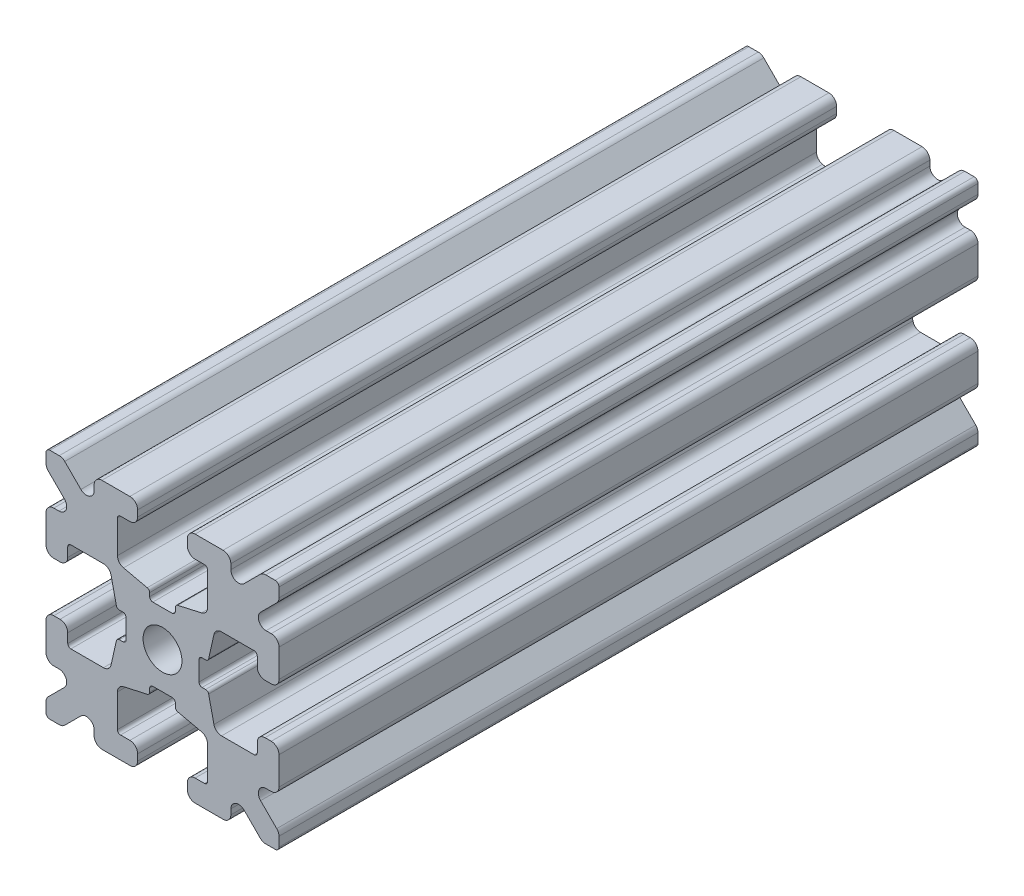
SolidWorks part; units mm, degrees
ref_plane "Front Plane" through (0, 0, 0) normal (0, 0, 1) x (1, 0, 0)
ref_plane "Top Plane" through (0, 0, 0) normal (0, 1, 0) x (1, 0, 0)
ref_plane "Right Plane" through (0, 0, 0) normal (1, 0, 0) x (0, 0, -1)
sketch "Sketch1" plane through (0, 0, 0) normal (0, 0, 1) x (1, 0, 0)
  line L1 (-7.5, -7.5) -> (7.5, -7.5)
  line L2 (-7.5, -7.5) -> (-7.5, 7.5)
  line L3 (-7.5, 7.5) -> (7.5, 7.5)
  line L4 (7.5, -7.5) -> (7.5, 7.5)
  line L5 (-7.5, -7.5) -> (7.5, 7.5) construction
  line L6 (-7.5, 7.5) -> (7.5, -7.5) construction
  circle A0 centre (0, 0) radius 1.25
  point P0 (0, 0)
  dimension "D2" = 2.5
  dimension "D1" = 15
extrude "Boss-Extrude1" add sketch "Sketch1" along normal mid plane 45
fillet "Fillet1" radius 0.25 4 edges at (7.5, -7.5, 0) (-7.5, -7.5, 0) (7.5, 7.5, 0) (-7.5, 7.5, 0)
sketch "Sketch2" plane through (0, 0, 22.5) normal (0, 0, 1) x (1, 0, 0)
  line L0 (-7.5, 7.25) -> (-7.5, -7.25) construction
  line L1 (-7.5, 1.6) -> (-6.1, 1.6)
  line L2 (-7.5, 1.6) -> (-7.5, -1.6)
  line L3 (-7.5, -1.6) -> (-6.1, -1.6)
  line L4 (-6.1, 1.6) -> (-6.1, 2.9)
  line L5 (0, 0) -> (-12.1036, 0) construction
  line L6 (-6.1, -2.9) -> (-3.4, -2.9)
  line L7 (0, 0) -> (-7.25, 7.25) construction
  line L8 (-6.1, 2.9) -> (-3.4, 2.9)
  line L9 (-3.4, -2.9) -> (-3.4, 2.9)
  line L10 (55, 0) -> (-55, 0) construction
  line L11 (-6.1, -2.9) -> (-6.1, -1.6)
  line L12 (2.9, 6.1) -> (1.6, 6.1)
  line L13 (2.9, 3.4) -> (-2.9, 3.4)
  line L14 (-2.9, 6.1) -> (-2.9, 3.4)
  line L15 (2.9, 6.1) -> (2.9, 3.4)
  line L16 (-1.6, 6.1) -> (-2.9, 6.1)
  line L17 (1.6, 7.5) -> (1.6, 6.1)
  line L18 (-1.6, 7.5) -> (1.6, 7.5)
  line L19 (-1.6, 7.5) -> (-1.6, 6.1)
  line L20 (-1.6, -7.5) -> (-1.6, -6.1)
  line L21 (-1.6, -7.5) -> (1.6, -7.5)
  line L22 (1.6, -7.5) -> (1.6, -6.1)
  line L23 (-1.6, -6.1) -> (-2.9, -6.1)
  line L24 (2.9, -6.1) -> (2.9, -3.4)
  line L25 (-2.9, -6.1) -> (-2.9, -3.4)
  line L26 (2.9, -3.4) -> (-2.9, -3.4)
  line L27 (2.9, -6.1) -> (1.6, -6.1)
  line L28 (6.1, -2.9) -> (6.1, -1.6)
  line L29 (3.4, -2.9) -> (3.4, 2.9)
  line L30 (6.1, 2.9) -> (3.4, 2.9)
  line L31 (6.1, -2.9) -> (3.4, -2.9)
  line L32 (6.1, 1.6) -> (6.1, 2.9)
  line L33 (7.5, -1.6) -> (6.1, -1.6)
  line L34 (7.5, 1.6) -> (7.5, -1.6)
  line L35 (7.5, 1.6) -> (6.1, 1.6)
  dimension "D1" = 3.2
  dimension "D2" = 5.8
  dimension "D3" = 1.4
  dimension "D4" = 2.7
extrude "Cut-Extrude1" cut sketch "Sketch2" against normal through all
sketch "Sketch4" plane through (0, 0, 22.5) normal (0, 0, 1) x (1, 0, 0)
  line L0 (-3.4, 2.9) -> (-2.75, 0)
  line L1 (55, 0) -> (-55, 0) construction
  line L2 (-2.75, 0) -> (-3.4, -2.9)
  line L3 (-3.4, -2.9) -> (-3.4, 2.9) construction
  line L4 (-3.4, 2.9) -> (-3.4, -2.9)
  line L5 (-2.9, 3.4) -> (0, 2.75)
  line L6 (0, 2.75) -> (2.9, 3.4)
  line L7 (2.9, 3.4) -> (-2.9, 3.4)
  line L8 (3.4, 2.9) -> (2.75, 0)
  line L9 (2.75, 0) -> (3.4, -2.9)
  line L10 (3.4, -2.9) -> (3.4, 2.9)
  line L11 (-2.9, -3.4) -> (0, -2.75)
  line L12 (0, -2.75) -> (2.9, -3.4)
  line L13 (2.9, -3.4) -> (-2.9, -3.4)
  circle A2 centre (0, 0) radius 2.75
  circle A3 centre (0, 0) radius 2.75 construction
  dimension "D1" = 1.5
extrude "Cut-Extrude3" cut sketch "Sketch4" against normal through all
fillet "Fillet3" radius 0.5 16 edges at (-6.1, -1.6, 0) (-7.5, -1.6, 0) (-6.1, 1.6, 0) (-7.5, 1.6, 0) (-1.6, -7.5, 0) (-1.6, -6.1, 0) (1.6, -7.5, 0) (1.6, -6.1, 0) (6.1, -1.6, 0) (7.5, -1.6, 0) (7.5, 1.6, 0) (6.1, 1.6, 0) (1.6, 7.5, 0) (1.6, 6.1, 0) (-1.6, 7.5, 0) (-1.6, 6.1, 0)
fillet "Fillet4" radius 0.5 8 edges at (-3.4, 2.9, 0) (-3.4, -2.9, 0) (2.9, -3.4, 0) (-2.9, -3.4, 0) (3.4, -2.9, 0) (3.4, 2.9, 0) (-2.9, 3.4, 0) (2.9, 3.4, 0)
fillet "Fillet5" radius 3 4 edges at (0, -2.75, 0) (2.75, 0, 0) (-2.75, 0, 0) (0, 2.75, 0)
fillet "Fillet6" radius 0.2 8 edges at (-2.9, -6.1, 0) (2.9, -6.1, 0) (6.1, -2.9, 0) (6.1, 2.9, 0) (2.9, 6.1, 0) (-2.9, 6.1, 0) (-6.1, -2.9, 0) (-6.1, 2.9, 0)
sketch "Sketch5" plane through (0, 0, 22.5) normal (0, 0, 1) x (1, 0, 0)
  line L0 (0, 0) -> (-7.25, 7.25) construction
  line L1 (-7.5, 6.4393) -> (-5.4607, 4.4)
  line L2 (-6.4393, 7.5) -> (-4.4, 5.4607)
  line L3 (-7.5, 4.4) -> (-5.4607, 4.4)
  line L4 (-3.8003, 2.9) -> (-5.9, 2.9) construction
  line L5 (0, 0) -> (-12.1819, 0) construction
  line L6 (-4.4, 7.5) -> (-4.4, 5.4607)
  line L7 (-2.9, 5.9) -> (-2.9, 3.8003) construction
  line L8 (-7.5, 6.4393) -> (-7.5, 4.4)
  line L9 (-7.5, 7.25) -> (-7.5, 2.1) construction
  line L10 (2.1, -7.5) -> (7.25, -7.5) construction
  line L11 (7.5, -7.25) -> (7.5, -2.1) construction
  line L12 (7.25, 7.5) -> (2.1, 7.5) construction
  line L13 (-2.1, 7.5) -> (-7.25, 7.5) construction
  line L14 (-4.4, 7.5) -> (-6.4393, 7.5)
  line L16 (55, 0) -> (-55, 0) construction
  line L17 (0, 0) -> (0, 10.993) construction
  line L18 (0, -54.6431) -> (0, 54.6431) construction
  line L20 (4.4, 7.5) -> (6.4393, 7.5)
  line L22 (7.5, 6.4393) -> (7.5, 4.4)
  line L23 (4.4, 7.5) -> (4.4, 5.4607)
  line L24 (7.5, 4.4) -> (5.4607, 4.4)
  line L25 (6.4393, 7.5) -> (4.4, 5.4607)
  line L26 (7.5, 6.4393) -> (5.4607, 4.4)
  line L27 (7.5, -6.4393) -> (5.4607, -4.4)
  line L28 (6.4393, -7.5) -> (4.4, -5.4607)
  line L29 (7.5, -4.4) -> (5.4607, -4.4)
  line L30 (4.4, -7.5) -> (4.4, -5.4607)
  line L31 (7.5, -6.4393) -> (7.5, -4.4)
  line L33 (4.4, -7.5) -> (6.4393, -7.5)
  line L36 (-4.4, -7.5) -> (-6.4393, -7.5)
  line L38 (-7.5, -6.4393) -> (-7.5, -4.4)
  line L39 (-4.4, -7.5) -> (-4.4, -5.4607)
  line L40 (-7.5, -4.4) -> (-5.4607, -4.4)
  line L41 (-6.4393, -7.5) -> (-4.4, -5.4607)
  line L42 (-7.5, -6.4393) -> (-5.4607, -4.4)
  dimension "D1" = 1.5
  dimension "D2" = 1.5
  dimension "D3" = 1.5
extrude "Cut-Extrude4" cut sketch "Sketch5" against normal through all
fillet "Fillet8" radius 0.5 24 edges at (-5.4607, 4.4, 0) (-7.5, 4.4, 0) (-5.4607, -4.4, 0) (-7.5, -4.4, 0) (-4.4, -7.5, 0) (-4.4, -5.4607, 0) (4.4, -7.5, 0) (4.4, -5.4607, 0) (5.4607, -4.4, 0) (7.5, -4.4, 0) (7.5, 4.4, 0) (5.4607, 4.4, 0) (4.4, 5.4607, 0) (4.4, 7.5, 0) (-4.4, 5.4607, 0) (-4.4, 7.5, 0) (-6.4393, 7.5, 0) (-7.5, 6.4393, 0) (6.4393, 7.5, 0) (7.5, 6.4393, 0) (6.4393, -7.5, 0) (7.5, -6.4393, 0) (-6.4393, -7.5, 0) (-7.5, -6.4393, 0)
sketch "Sketch6" plane through (0, 0, 22.5) normal (0, 0, 1) x (1, 0, 0)
  line L0 (0, 0) -> (0, 11.013) construction
  line L1 (0.6561, 2.8971) -> (2.1235, 2.8971) construction
  line L2 (0, -54.6431) -> (0, 54.6431) construction
  line L3 (0, 0) -> (7.25, 7.25) construction
  line L4 (7.5, 0.8255) -> (7.5, -0.8255)
  line L5 (2.3471, 0.8255) -> (7.5, 0.8255)
  line L6 (0, 0) -> (12.4016, 0) construction
  line L7 (0.8255, -7.5) -> (-0.8255, -7.5)
  line L8 (2.3471, -0.8255) -> (2.3471, 0.8255)
  line L9 (0.8255, -2.3471) -> (0.8255, -7.5)
  line L10 (7.5, -0.8255) -> (2.3471, -0.8255)
  line L11 (-7.5, -0.8255) -> (-2.3471, -0.8255)
  line L12 (-2.3471, -0.8255) -> (-2.3471, 0.8255)
  line L13 (-0.8255, -2.3471) -> (0.8255, -2.3471)
  line L14 (-0.8255, 7.5) -> (-0.8255, 2.3471)
  line L15 (-0.8255, 2.3471) -> (0.8255, 2.3471)
  line L16 (-0.8255, -7.5) -> (-0.8255, -2.3471)
  line L17 (0.8255, 2.3471) -> (0.8255, 7.5)
  line L18 (0.8255, 7.5) -> (-0.8255, 7.5)
  line L19 (3.9, 7.5) -> (2.1, 7.5) construction
  line L20 (-2.3471, 0.8255) -> (-7.5, 0.8255)
  line L21 (-7.5, 0.8255) -> (-7.5, -0.8255)
  point P5 (0, -2.5973)
  point P7 (0, 2.5973)
  dimension "D3" = 0.55
  dimension "D1" = 1.651
extrude "Cut-Extrude5" cut sketch "Sketch6" against normal through all
fillet "Fillet10" radius 0.2 16 edges at (-2.935, 0.8255, 0) (-2.935, -0.8255, 0) (2.935, -0.8255, 0) (2.935, 0.8255, 0) (0.8255, 2.935, 0) (-0.8255, 2.935, 0) (-2.3471, 0.8255, 0) (-2.3471, -0.8255, 0) (0.8255, 2.3471, 0) (-0.8255, 2.3471, 0) (2.3471, 0.8255, 0) (2.3471, -0.8255, 0) (0.8255, -2.935, 0) (0.8255, -2.3471, 0) (-0.8255, -2.3471, 0) (-0.8255, -2.935, 0)
